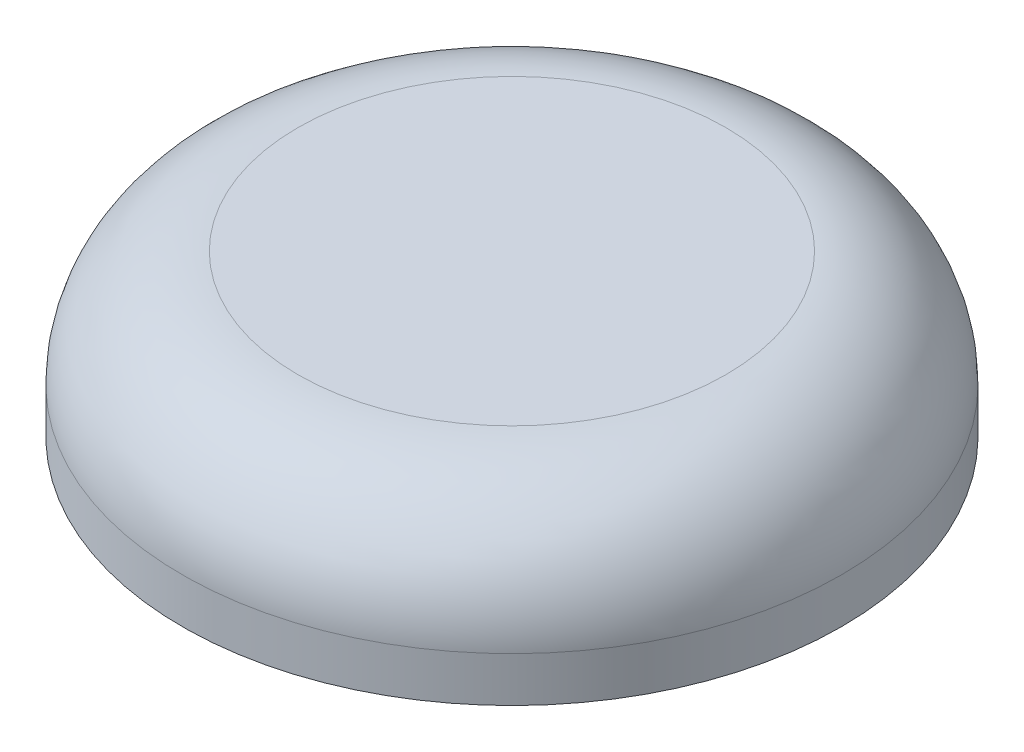
SolidWorks part; units mm, degrees
ref_plane "Front Plane" through (0, 0, 0) normal (0, 0, 1) x (1, 0, 0)
ref_plane "Top Plane" through (0, 0, 0) normal (0, 1, 0) x (1, 0, 0)
ref_plane "Right Plane" through (0, 0, 0) normal (1, 0, 0) x (0, 0, -1)
sketch "Sketch1" plane through (0, 0, 0) normal (0, 0, 1) x (1, 0, 0)
  line L0 (-12.065, 0) -> (-12.065, -8.382)
  line L1 (0, 0) -> (-12.065, 0)
  line L2 (-12.065, -8.382) -> (-19.558, -8.382)
  line L3 (0, 0) -> (0, 1.143)
  line L4 (0, 1.143) -> (-12.7, 1.143)
  line L5 (-19.558, -8.382) -> (-19.558, -5.715)
  arc A0 (-19.558, -5.715) -> (-12.7, 1.143) centre (-12.7, -5.715) cw
  point P9 (-14.4429, 1.143)
  dimension "D1" = 9.525
  dimension "D2" = 19.558
  dimension "D3" = 12.065
  dimension "D4" = 8.382
  dimension "D5" = 12.7
revolve "Revolve1" add sketch "Sketch1" angle 360 about L3
